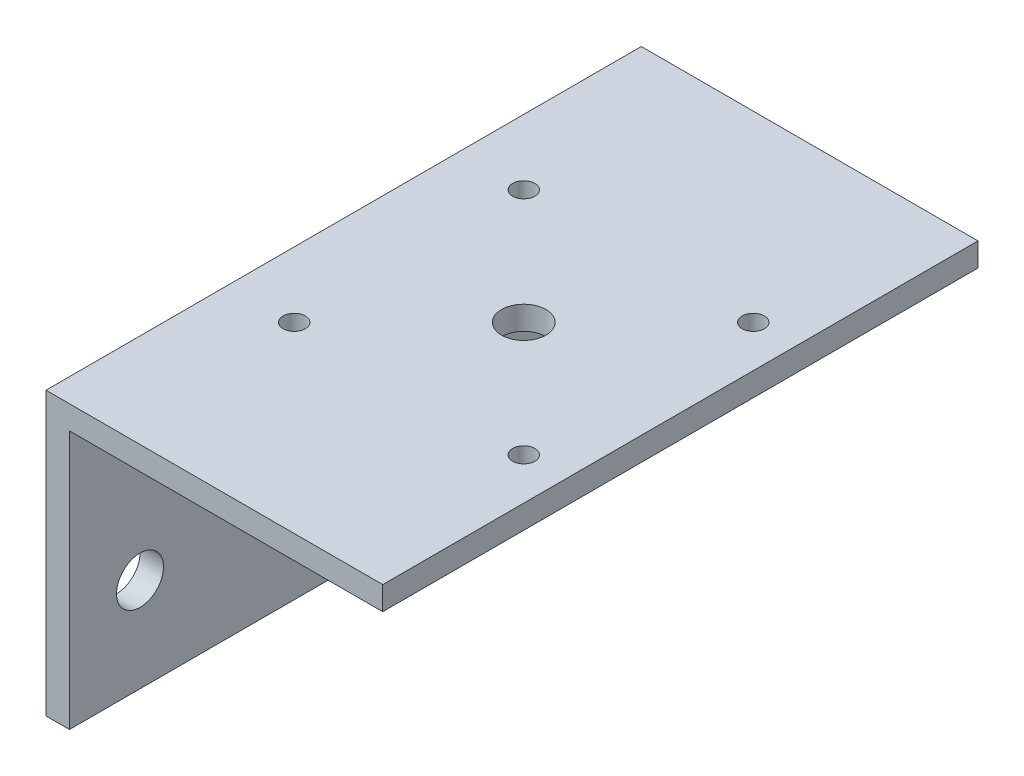
SolidWorks part; units mm, degrees
ref_plane "Front Plane" through (0, 0, 0) normal (0, 0, 1) x (1, 0, 0)
ref_plane "Top Plane" through (0, 0, 0) normal (0, 1, 0) x (1, 0, 0)
ref_plane "Right Plane" through (0, 0, 0) normal (1, 0, 0) x (0, 0, -1)
sketch "Sketch1" plane through (0, 0, 0) normal (0, 0, 1) x (1, 0, 0)
  line L1 (0, 0) -> (3.175, 0)
  line L2 (0, 0) -> (0, 38.1)
  line L3 (0, 38.1) -> (45.475, 38.1)
  line L4 (45.475, 34.925) -> (45.475, 38.1)
  line L7 (45.475, 34.925) -> (3.175, 34.925)
  line L8 (3.175, 0) -> (3.175, 34.925)
  dimension "D1" = 38.1
  dimension "D2" = 45.475
  dimension "D3" = 3.175
  dimension "D4" = 3.175
extrude "Boss-Extrude1" add sketch "Sketch1" along normal blind 80.4
sketch "Sketch2" plane through (3.175, 0, 0) normal (1, 0, 0) x (0, 0, -1)
  line L0 (-80.4, 0) -> (0, 0) construction
  line L1 (0, 0) -> (0, 34.925) construction
  line L2 (-80.4, 0) -> (-80.4, 34.925) construction
  circle A0 centre (-70.875, 12.7) radius 3.175
  circle A1 centre (-9.525, 12.7) radius 3.175
  dimension "D1" = 6.35
  dimension "D2" = 12.7
  dimension "D3" = 12.7
  dimension "D4" = 9.525
  dimension "D5" = 9.525
extrude "Cut-Extrude1" cut sketch "Sketch2" against normal through all
sketch "Sketch3" plane through (0, 38.1, 0) normal (0, 1, 0) x (1, 0, 0)
  line L0 (0, -40.2) -> (45.475, -40.2) construction
  line L1 (0, -80.4) -> (0, 0) construction
  line L2 (45.475, -80.4) -> (45.475, 0) construction
  line L3 (24.325, -80.4) -> (24.325, 0) construction
  line L4 (45.475, -80.4) -> (0, -80.4) construction
  line L5 (45.475, 0) -> (0, 0) construction
  circle A0 centre (39.825, -55.7) radius 1.5
  circle A1 centre (8.825, -55.7) radius 1.5
  circle A2 centre (8.825, -24.7) radius 1.5
  circle A3 centre (39.825, -24.7) radius 1.5
  circle A4 centre (24.325, -40.2) radius 3
  dimension "D1" = 3
  dimension "D7" = 6
  dimension "D2" = 31
  dimension "D3" = 31
  dimension "D4" = 15.5
  dimension "D5" = 21.15
  dimension "D6" = 15.5
extrude "Cut-Extrude2" cut sketch "Sketch3" against normal through all
